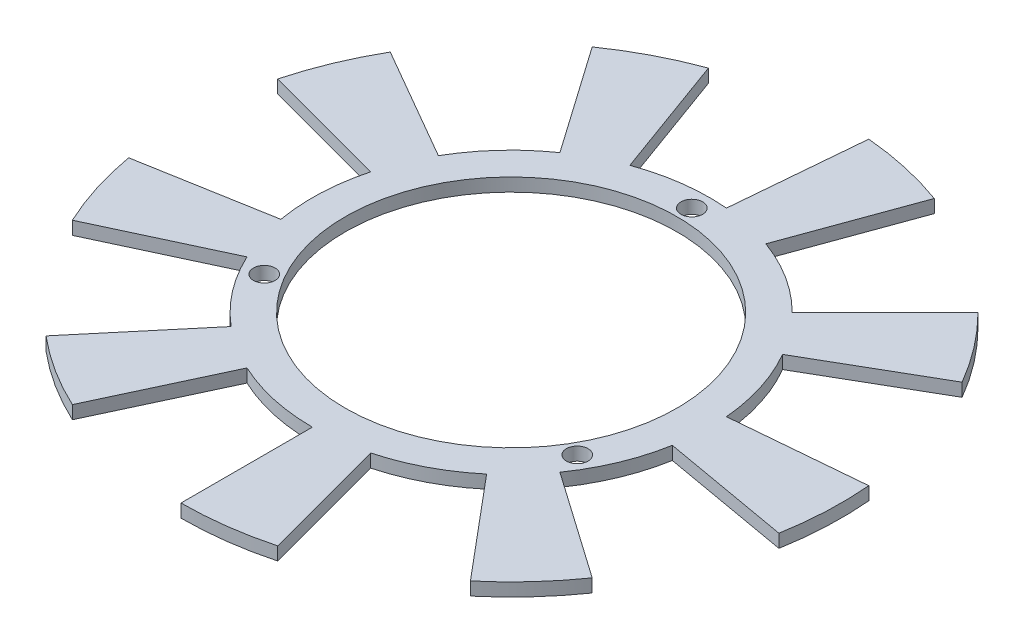
SolidWorks part; units mm, degrees
material "AISI 1010 Steel, hot rolled bar"
ref_plane "Front Plane" through (0, 0, 0) normal (0, 0, 1) x (1, 0, 0)
ref_plane "Top Plane" through (0, 0, 0) normal (0, 1, 0) x (1, 0, 0)
ref_plane "Right Plane" through (0, 0, 0) normal (1, 0, 0) x (0, 0, -1)
sketch "Sketch1" plane through (0, 0, 0) normal (0, 1, 0) x (1, 0, 0)
  circle A0 centre (0, 0) radius 25.25
  dimension "D1" = 50.5
extrude "Extrude-Thin1" add sketch "Sketch1" against normal blind 2 thin
sketch "Sketch2" plane through (0, 0, 0) normal (0, 1, 0) x (1, 0, 0)
  line L0 (0, -30.25) -> (0, 30.25) construction
  line L1 (0, 0) -> (23.8157, -13.75) construction
  line L2 (0, 0) -> (-23.8157, -13.75) construction
  circle A0 centre (0, 27.5) radius 1.65
  circle A1 centre (0, 0) radius 30.25 construction
  circle A4 centre (0, 0) radius 27.5 construction
  circle A7 centre (23.8157, -13.75) radius 1.65
  circle A8 centre (-23.8157, -13.75) radius 1.65
  dimension "D1" = 55
  dimension "D2" = 3.3
  dimension "D3" = 120
  dimension "D4" = 120
extrude "Cut-Extrude3" cut sketch "Sketch2" against normal blind 10
sketch "Sketch5" plane through (0, -2, 0) normal (0, -1, 0) x (1, 0, 0)
  line L0 (0, 0) -> (0, 35.9971) construction
  line L1 (0, 0) -> (8.8275, 32.9446) construction
  line L2 (0, 50.25) -> (0, 30.25)
  line L3 (7.8293, 29.2193) -> (13.0057, 48.5378)
  line L4 (32.3001, 38.4937) -> (19.4443, 23.1728)
  line L5 (24.7793, 17.3507) -> (41.1624, 28.8222)
  line L6 (49.4866, 8.7258) -> (29.7904, 5.2529)
  line L7 (30.1349, -2.6365) -> (50.0588, -4.3796)
  line L8 (43.5178, -25.125) -> (26.1973, -15.125)
  line L9 (21.39, -21.39) -> (35.5321, -35.5321)
  line L10 (17.1865, -47.2196) -> (10.3461, -28.4257)
  line L11 (2.6365, -30.1349) -> (4.3796, -50.0588)
  line L12 (-17.1865, -47.2196) -> (-10.3461, -28.4257)
  line L13 (-17.3507, -24.7793) -> (-28.8222, -41.1624)
  line L14 (-43.5178, -25.125) -> (-26.1973, -15.125)
  line L15 (-29.2193, -7.8293) -> (-48.5378, -13.0057)
  line L16 (-49.4866, 8.7258) -> (-29.7904, 5.2529)
  line L17 (-27.4158, 12.7842) -> (-45.542, 21.2366)
  line L18 (-32.3001, 38.4937) -> (-19.4443, 23.1728)
  line L19 (-12.7842, 27.4158) -> (-21.2366, 45.542)
  circle A0 centre (0, 0) radius 30.25 construction
  arc A1 (7.8293, 29.2193) -> (0, 30.25) centre (0, 0) ccw
  arc A2 (13.0057, 48.5378) -> (0, 50.25) centre (0, 0) ccw
  arc A3 (41.1624, 28.8222) -> (32.3001, 38.4937) centre (0, 0) ccw
  arc A4 (24.7793, 17.3507) -> (19.4443, 23.1728) centre (0, 0) ccw
  arc A5 (50.0588, -4.3796) -> (49.4866, 8.7258) centre (0, 0) ccw
  arc A6 (30.1349, -2.6365) -> (29.7904, 5.2529) centre (0, 0) ccw
  arc A7 (35.5321, -35.5321) -> (43.5178, -25.125) centre (0, 0) ccw
  arc A8 (21.39, -21.39) -> (26.1973, -15.125) centre (0, 0) ccw
  arc A9 (4.3796, -50.0588) -> (17.1865, -47.2196) centre (0, 0) ccw
  arc A10 (2.6365, -30.1349) -> (10.3461, -28.4257) centre (0, 0) ccw
  arc A11 (-28.8222, -41.1624) -> (-17.1865, -47.2196) centre (0, 0) ccw
  arc A12 (-17.3507, -24.7793) -> (-10.3461, -28.4257) centre (0, 0) ccw
  arc A13 (-48.5378, -13.0057) -> (-43.5178, -25.125) centre (0, 0) ccw
  arc A14 (-29.2193, -7.8293) -> (-26.1973, -15.125) centre (0, 0) ccw
  arc A15 (-45.542, 21.2366) -> (-49.4866, 8.7258) centre (0, 0) ccw
  arc A16 (-27.4158, 12.7842) -> (-29.7904, 5.2529) centre (0, 0) ccw
  arc A17 (-21.2366, 45.542) -> (-32.3001, 38.4937) centre (0, 0) ccw
  arc A18 (-12.7842, 27.4158) -> (-19.4443, 23.1728) centre (0, 0) ccw
  point P87 (0, 0)
  dimension "D2" = 20
  dimension "D1" = 15
  dimension "D3" = 9
extrude "Boss-Extrude1" add sketch "Sketch5" against normal blind 2
